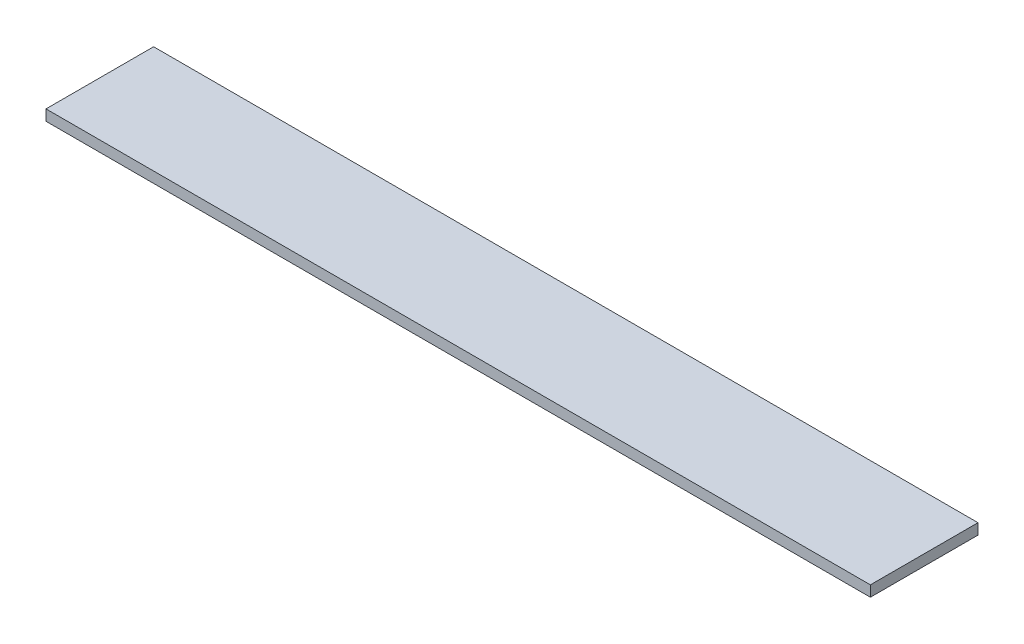
SolidWorks part; units mm, degrees
ref_plane "Face" through (0, 0, 0) normal (0, 0, 1) x (1, 0, 0)
ref_plane "Dessus" through (0, 0, 0) normal (0, 1, 0) x (1, 0, 0)
ref_plane "Droite" through (0, 0, 0) normal (1, 0, 0) x (0, 0, -1)
sketch "Esquisse1" plane through (0, 0, 0) normal (0, 1, 0) x (1, 0, 0)
  line L1 (0, 0) -> (766, 0)
  line L2 (0, 0) -> (0, 100)
  line L3 (0, 100) -> (766, 100)
  line L4 (766, 0) -> (766, 100)
  dimension "D1" = 766
  dimension "D2" = 100
extrude "Extrusion1" add sketch "Esquisse1" along normal blind 10
